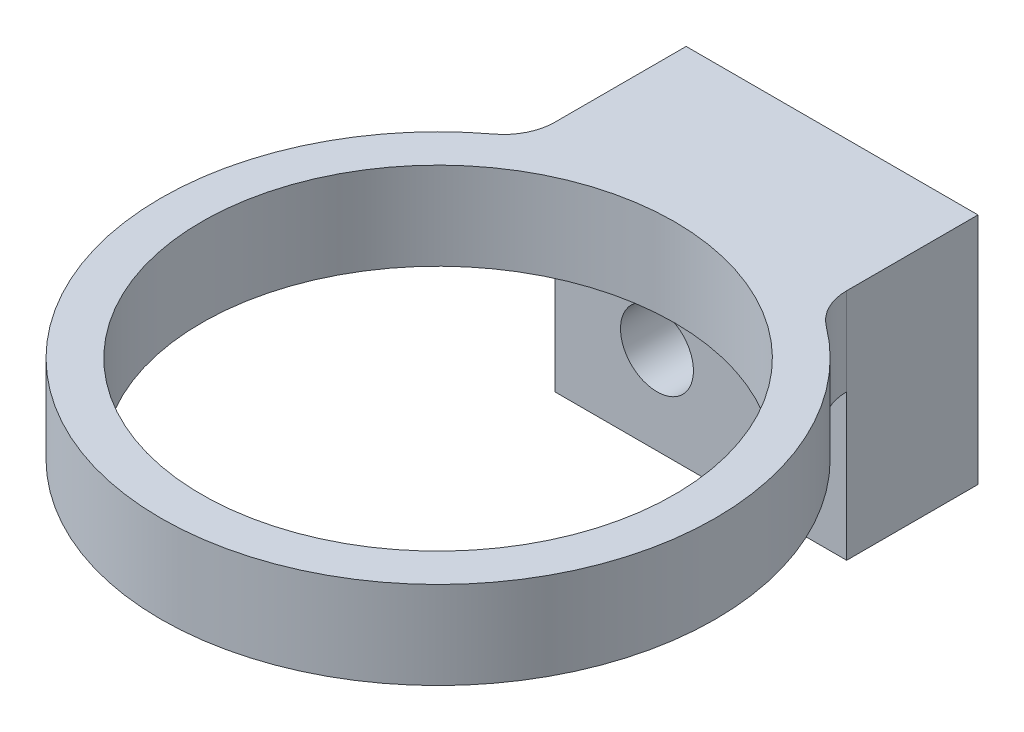
SolidWorks part; units mm, degrees
ref_plane "Front Plane" through (0, 0, 0) normal (0, 0, 1) x (1, 0, 0)
ref_plane "Top Plane" through (0, 0, 0) normal (0, 1, 0) x (1, 0, 0)
ref_plane "Right Plane" through (0, 0, 0) normal (1, 0, 0) x (0, 0, -1)
ref_plane "Plane1" through (0, 0, 0) normal (0, -1, 0) x (1, 0, 0)
sketch "Sketch1" plane through (0, 0, 0) normal (0, -1, 0) x (1, 0, 0)
  line L0 (-5, 5.4223) -> (-5, 0)
  line L1 (-5, 0) -> (5, 0)
  line L2 (5, 0) -> (5, 5.4223)
  arc A0 (5, 5.4223) -> (-5, 5.4223) centre (0, 13.5) ccw
extrude "Boss-Extrude1" add sketch "Sketch1" against normal blind 3
sketch "Sketch2" plane through (0, 0, 0) normal (0, -1, 0) x (1, 0, 0)
  line L0 (-5, 0) -> (-5, 4.5)
  line L1 (-5, 4.5) -> (5, 4.5)
  line L2 (5, 4.5) -> (5, 0)
  line L3 (5, 0) -> (-5, 0)
extrude "Boss-Extrude2" add sketch "Sketch2" along normal blind 5
hole_wizard "Ø1.6 (1.6) Diameter Hole1" positions "Sketch4" profile "Sketch3" hole size "Ø1.6" standard "ANSI Metric"
sketch "Sketch4" plane through (0, 0, 0) normal (0, 0, -1) x (-1, 0, 0)
  point P0 (-3, 1)
sketch "Sketch3" plane through (3, 1, 0) normal (1, 0, 0) x (0, 1, 0)
  line L0 (0, 0) -> (0, 4.4807)
  line L1 (0, 4.4807) -> (0.8, 4)
  line L2 (0.8, 4) -> (0.8, 0)
  line L5 (0.8, 0) -> (0, 0)
  line L10 (0, 4.4807) -> (-0.8, 4) construction
  line L11 (0, -6.35) -> (0, 107.95) construction
  dimension "Hole Dia." = 1.6
  dimension "Hole Depth" = 4
  dimension "Drill Angle" = 118
hole_wizard "Ø2.5 (2.5) Diameter Hole1" positions "Sketch6" profile "Sketch5" hole size "Ø2.5" standard "ANSI Metric"
sketch "Sketch6" plane through (0, 0, 4.5) normal (0, 0, 1) x (1, 0, 0)
  point P0 (-1.5, -2)
sketch "Sketch5" plane through (-1.5, -2, 4.5) normal (1, 0, 0) x (0, -1, 0)
  line L0 (0, 0) -> (0, 4.5)
  line L1 (0, 4.5) -> (1.25, 4.5)
  line L2 (1.25, 4.5) -> (1.25, 0)
  line L5 (1.25, 0) -> (0, 0)
  line L11 (0, -6.35) -> (0, 107.95) construction
  dimension "Thru Hole Dia." = 2.5
  dimension "Thru Hole Depth" = 4.5
hole_wizard "M14 Clearance Hole1" positions "Sketch8" profile "Sketch7" hole size "M14" standard "ANSI Metric"
sketch "Sketch8" plane through (0, 0, 0) normal (0, -1, 0) x (-1, 0, 0)
  point P0 (0, -13.5)
sketch "Sketch7" plane through (0, 0, 13.5) normal (1, 0, 0) x (0, 0, -1)
  line L0 (0, 0) -> (0, 3)
  line L1 (0, 3) -> (8.1, 3)
  line L2 (8.1, 3) -> (8.1, 0)
  line L5 (8.1, 0) -> (0, 0)
  line L11 (0, -6.35) -> (0, 107.95) construction
  dimension "Thru Hole Dia." = 16.2
  dimension "Thru Hole Depth" = 3
fillet "Fillet1" radius 1.75 2 edges at (-5, 1.5, 5.4223) (5, 1.5, 5.4223)
